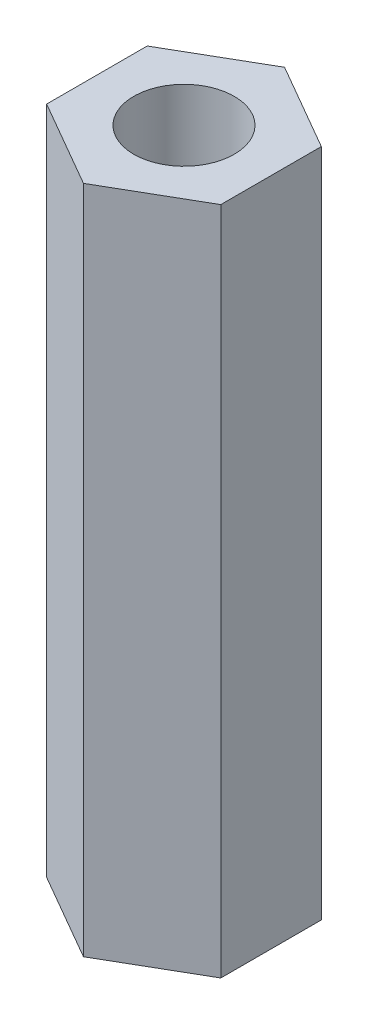
SolidWorks part; units mm, degrees
ref_plane "Front Plane" through (0, 0, 0) normal (0, 0, 1) x (1, 0, 0)
ref_plane "Top Plane" through (0, 0, 0) normal (0, 1, 0) x (1, 0, 0)
ref_plane "Right Plane" through (0, 0, 0) normal (1, 0, 0) x (0, 0, -1)
sketch "Sketch1" plane through (0, 0, 0) normal (0, 1, 0) x (1, 0, 0)
  line L0 (0, 0) -> (2.6, 0) construction
  line L1 (0, 3.0022) -> (-2.6, 1.5011)
  line L2 (-2.6, 1.5011) -> (-2.6, -1.5011)
  line L3 (-2.6, -1.5011) -> (0, -3.0022)
  line L4 (0, -3.0022) -> (2.6, -1.5011)
  line L5 (2.6, -1.5011) -> (2.6, 1.5011)
  line L6 (2.6, 1.5011) -> (0, 3.0022)
  circle A0 centre (0, 0) radius 1.5
  circle A1 centre (0, 0) radius 2.6 construction
  dimension "D1" = 3
  dimension "D2" = 2.6
extrude "Boss-Extrude2" add sketch "Sketch1" along normal blind 20
